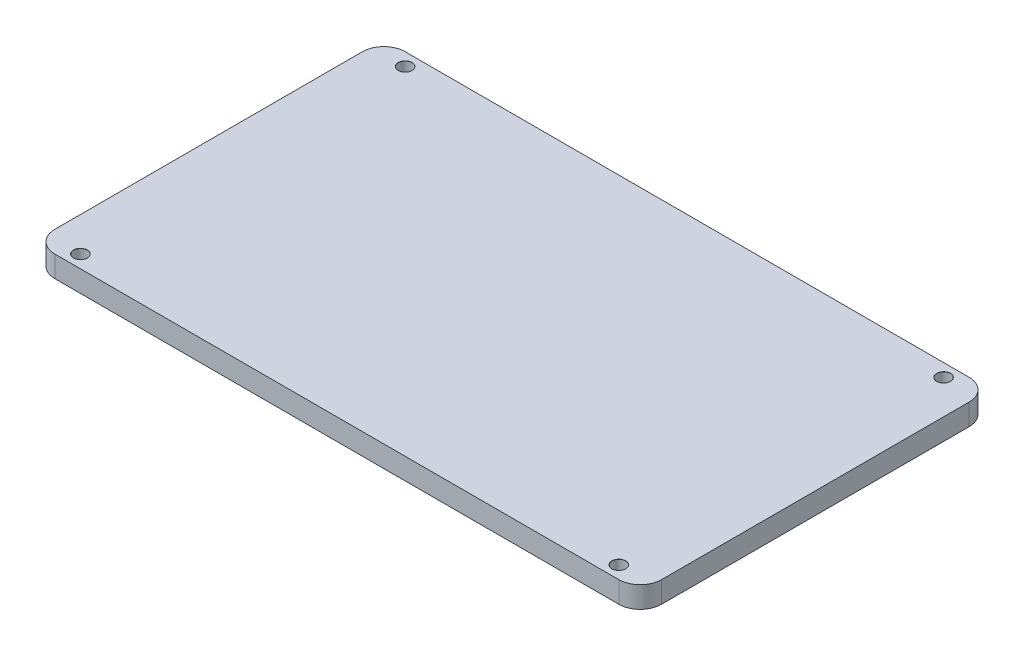
SolidWorks part; units mm, degrees
ref_plane "前视基准面" through (0, 0, 0) normal (0, 0, 1) x (1, 0, 0)
ref_plane "上视基准面" through (0, 0, 0) normal (0, 1, 0) x (1, 0, 0)
ref_plane "右视基准面" through (0, 0, 0) normal (1, 0, 0) x (0, 0, -1)
sketch "Sketch1" plane through (0, 0, 0) normal (0, 1, 0) x (1, 0, 0)
  line L1 (-71, -41) -> (71, -41)
  line L2 (-71, -41) -> (-71, 41)
  line L3 (-71, 41) -> (71, 41)
  line L4 (71, -41) -> (71, 41)
  line L5 (-71, -41) -> (71, 41) construction
  line L6 (-71, 41) -> (71, -41) construction
  point P0 (0, 0)
  dimension "D1" = 142
  dimension "D2" = 82
extrude "Boss-Extrude1" add sketch "Sketch1" along normal blind 5
hole_wizard "M3 Clearance Hole1" positions "Sketch2" profile "Sketch3" hole size "M3" standard "GB" end condition through all
sketch "Sketch2" plane through (0, 5, 0) normal (0, 1, 0) x (1, 0, 0)
  line L0 (71, 41) -> (-71, 41) construction
  line L1 (-71, 41) -> (-71, -41) construction
  line L2 (-71, -41) -> (71, -41) construction
  line L3 (71, -41) -> (71, 41) construction
  point P0 (-63, 38)
  point P2 (-63, -38)
  point P4 (63, 38)
  point P6 (63, -38)
  dimension "D1" = 3
  dimension "D2" = 8
  dimension "D3" = 3
  dimension "D4" = 8
  dimension "D5" = 3
  dimension "D6" = 8
  dimension "D7" = 8
  dimension "D8" = 3
sketch "Sketch3" plane through (-63, 5, -38) normal (1, 0, 0) x (0, 0, 1)
  line L0 (0, 0) -> (0, 5)
  line L1 (0, 5) -> (1.6, 5)
  line L2 (1.6, 5) -> (1.6, 0.025)
  line L3 (1.6, 0.025) -> (1.625, 0)
  line L5 (1.625, 0) -> (0, 0)
  line L6 (-1.6, 0.025) -> (-1.625, 0) construction
  line L11 (0, -6.35) -> (0, 107.95) construction
  dimension "Thru Hole Dia." = 3.2
  dimension "Thru Hole Depth" = 5
  dimension "Near C'Sink Dia." = 3.25
  dimension "Near C'Sink Angle" = 90
fillet "Fillet1" radius 5 4 edges at (71, 2.5, -41) (71, 2.5, 41) (-71, 2.5, 41) (-71, 2.5, -41)
